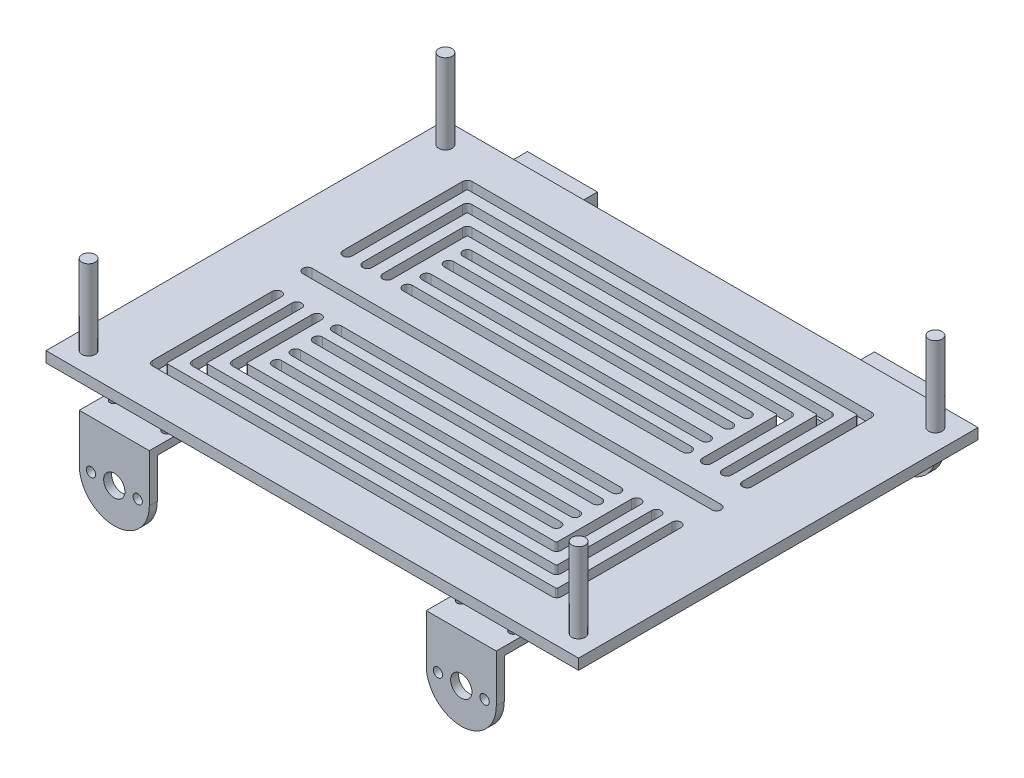
SolidWorks part; units mm, degrees
ref_plane "前基準面" through (0, 0, 0) normal (0, 0, 1) x (1, 0, 0)
ref_plane "上基準面" through (0, 0, 0) normal (0, 1, 0) x (1, 0, 0)
ref_plane "右基準面" through (0, 0, 0) normal (1, 0, 0) x (0, 0, -1)
sketch "草圖1" plane through (0, 0, 0) normal (0, 1, 0) x (1, 0, 0)
  line L0 (0.0511, 0) -> (-99.9489, 0) construction
  line L7 (-99.9489, 75) -> (100.0511, 75)
  line L8 (-99.9489, 75) -> (-99.9489, -75)
  line L9 (-99.9489, -75) -> (100.0511, -75)
  line L10 (100.0511, 75) -> (100.0511, -75)
  line L13 (0.0511, 0) -> (0.0511, 75) construction
  line L14 (-75, 58.25) -> (79.7717, 58.25) construction
  line L15 (-75, 60) -> (75.1022, 60)
  line L16 (-72.75, 56.5) -> (72.8522, 56.5)
  line L17 (-75, 58.25) -> (-75, 13.25) construction
  line L20 (-52.4456, -35.75) -> (52.4456, -35.75) construction
  line L23 (75.1022, 58.25) -> (75.1022, 13.25) construction
  line L29 (-73.25, 56) -> (-73.25, 13.25)
  line L30 (-76.75, 58.25) -> (-76.75, 13.25)
  line L35 (-52.4456, -37.5) -> (52.4456, -37.5)
  line L38 (-67.5, 50.75) -> (67.5, 50.75) construction
  line L39 (-67.5, 52.5) -> (67.5, 52.5)
  line L40 (-65.25, 49) -> (65.25, 49)
  line L41 (-67.5, 50.75) -> (-67.5, 13.25) construction
  line L42 (-65.75, 48.5) -> (-65.75, 13.25)
  line L43 (-69.25, 50.75) -> (-69.25, 13.25)
  line L44 (67.5, 50.75) -> (67.5, 13.25) construction
  line L45 (69.25, 50.75) -> (69.25, 13.25)
  line L46 (65.75, 48.5) -> (65.75, 13.25)
  line L47 (-60, 43.25) -> (60, 43.25) construction
  line L48 (-60, 45) -> (60, 45)
  line L49 (-57.75, 41.5) -> (57.75, 41.5)
  line L50 (-60, 43.25) -> (-60, 13.25) construction
  line L51 (-58.25, 41) -> (-58.25, 13.25)
  line L52 (-61.75, 43.25) -> (-61.75, 13.25)
  line L53 (60, 43.25) -> (60, 13.25) construction
  line L54 (61.75, 43.25) -> (61.75, 13.25)
  line L55 (58.25, 41) -> (58.25, 13.25)
  line L56 (-52.4456, 35.75) -> (52.4456, 35.75) construction
  line L57 (-52.4456, 37.5) -> (52.4456, 37.5)
  line L58 (-52.4456, 34) -> (52.4456, 34)
  line L59 (-52.4456, 28.75) -> (52.4456, 28.75) construction
  line L60 (-52.4456, 30.5) -> (52.4456, 30.5)
  line L61 (-52.4456, 27) -> (52.4456, 27)
  line L62 (-52.4456, 20.4169) -> (52.4456, 20.4169) construction
  line L63 (-52.4456, 22.1669) -> (52.4456, 22.1669)
  line L64 (-52.4456, 18.6669) -> (52.4456, 18.6669)
  line L65 (-52.4456, 13.25) -> (52.4456, 13.25) construction
  line L66 (-52.4456, 15) -> (52.4456, 15)
  line L67 (-52.4456, 11.5) -> (52.4456, 11.5)
  line L68 (76.8522, 58.25) -> (76.8522, 13.25)
  line L69 (73.3522, 56) -> (73.3522, 13.25)
  line L70 (-52.4456, -34) -> (52.4456, -34)
  line L71 (-52.4456, -28.75) -> (52.4456, -28.75) construction
  line L72 (-52.4456, -30.5) -> (52.4456, -30.5)
  line L73 (-52.4456, -27) -> (52.4456, -27)
  line L74 (-52.4456, -20.4169) -> (52.4456, -20.4169) construction
  line L75 (-52.4456, -22.1669) -> (52.4456, -22.1669)
  line L76 (-52.4456, -18.6669) -> (52.4456, -18.6669)
  line L77 (-52.4456, -13.25) -> (52.4456, -13.25) construction
  line L78 (-52.4456, -15) -> (52.4456, -15)
  line L79 (-52.4456, -11.5) -> (52.4456, -11.5)
  line L80 (76.8522, -58.25) -> (76.8522, -13.25)
  line L81 (73.3522, -56) -> (73.3522, -13.25)
  line L82 (69.25, -50.75) -> (69.25, -13.25)
  line L83 (65.75, -48.5) -> (65.75, -13.25)
  line L84 (61.75, -43.25) -> (61.75, -13.25)
  line L85 (58.25, -41) -> (58.25, -13.25)
  line L86 (-67.5, -52.5) -> (67.5, -52.5)
  line L87 (-65.25, -49) -> (65.25, -49)
  line L88 (-60, -45) -> (60, -45)
  line L89 (-57.75, -41.5) -> (57.75, -41.5)
  line L90 (-69.25, -50.75) -> (-69.25, -13.25)
  line L91 (-65.75, -48.5) -> (-65.75, -13.25)
  line L92 (-61.75, -43.25) -> (-61.75, -13.25)
  line L93 (-58.25, -41) -> (-58.25, -13.25)
  line L94 (-73.25, -56) -> (-73.25, -13.25)
  line L95 (-72.75, -56.5) -> (72.8522, -56.5)
  line L96 (-75, -60) -> (75.1022, -60)
  line L97 (-76.75, -58.25) -> (-76.75, -13.25)
  line L98 (-76.75, 0) -> (76.8522, 0) construction
  line L99 (-76.75, 1.75) -> (76.8522, 1.75)
  line L100 (-76.75, -1.75) -> (76.8522, -1.75)
  circle A0 centre (-91.9489, 67) radius 1.5
  circle A1 centre (-91.9489, -67) radius 1.5
  circle A2 centre (92.0511, -67) radius 1.5
  circle A3 centre (92.0511, 67) radius 1.5
  arc A4 (-75, 60) -> (-76.75, 58.25) centre (-75, 58.25) ccw
  arc A14 (-75, 60) -> (-76.75, 58.25) centre (-75, 58.25) ccw
  arc A15 (-76.75, 13.25) -> (-73.25, 13.25) centre (-75, 13.25) ccw
  arc A22 (-73.25, 56) -> (-72.75, 56.5) centre (-72.75, 56) cw
  arc A24 (-52.4456, -37.5) -> (-52.4456, -34) centre (-52.4456, -35.75) cw
  arc A25 (52.4456, -34) -> (52.4456, -37.5) centre (52.4456, -35.75) cw
  arc A26 (-67.5, 52.5) -> (-69.25, 50.75) centre (-67.5, 50.75) ccw
  arc A27 (69.25, 50.75) -> (67.5, 52.5) centre (67.5, 50.75) ccw
  arc A28 (-67.5, 52.5) -> (-69.25, 50.75) centre (-67.5, 50.75) ccw
  arc A29 (-69.25, 13.25) -> (-65.75, 13.25) centre (-67.5, 13.25) ccw
  arc A30 (69.25, 50.75) -> (67.5, 52.5) centre (67.5, 50.75) ccw
  arc A31 (65.75, 13.25) -> (69.25, 13.25) centre (67.5, 13.25) ccw
  arc A32 (-60, 45) -> (-61.75, 43.25) centre (-60, 43.25) ccw
  arc A33 (61.75, 43.25) -> (60, 45) centre (60, 43.25) ccw
  arc A34 (-60, 45) -> (-61.75, 43.25) centre (-60, 43.25) ccw
  arc A35 (-61.75, 13.25) -> (-58.25, 13.25) centre (-60, 13.25) ccw
  arc A36 (61.75, 43.25) -> (60, 45) centre (60, 43.25) ccw
  arc A37 (58.25, 13.25) -> (61.75, 13.25) centre (60, 13.25) ccw
  arc A38 (-52.4456, 37.5) -> (-52.4456, 34) centre (-52.4456, 35.75) ccw
  arc A39 (52.4456, 34) -> (52.4456, 37.5) centre (52.4456, 35.75) ccw
  arc A40 (-52.4456, 30.5) -> (-52.4456, 27) centre (-52.4456, 28.75) ccw
  arc A41 (52.4456, 27) -> (52.4456, 30.5) centre (52.4456, 28.75) ccw
  arc A42 (-52.4456, 22.1669) -> (-52.4456, 18.6669) centre (-52.4456, 20.4169) ccw
  arc A43 (52.4456, 18.6669) -> (52.4456, 22.1669) centre (52.4456, 20.4169) ccw
  arc A44 (-52.4456, 15) -> (-52.4456, 11.5) centre (-52.4456, 13.25) ccw
  arc A45 (52.4456, 11.5) -> (52.4456, 15) centre (52.4456, 13.25) ccw
  arc A47 (75.1022, 60) -> (76.8522, 58.25) centre (75.1022, 58.25) cw
  arc A48 (76.8522, 58.25) -> (75.1022, 60) centre (75.1022, 58.25) ccw
  arc A49 (73.3522, 13.25) -> (76.8522, 13.25) centre (75.1022, 13.25) ccw
  arc A50 (-65.75, 48.5) -> (-65.25, 49) centre (-65.25, 48.5) cw
  arc A51 (-58.25, 41) -> (-57.75, 41.5) centre (-57.75, 41) cw
  arc A52 (58.25, 41) -> (57.75, 41.5) centre (57.75, 41) ccw
  arc A53 (65.75, 48.5) -> (65.25, 49) centre (65.25, 48.5) ccw
  arc A54 (73.3522, 56) -> (72.8522, 56.5) centre (72.8522, 56) ccw
  arc A55 (-52.4456, -30.5) -> (-52.4456, -27) centre (-52.4456, -28.75) cw
  arc A56 (52.4456, -27) -> (52.4456, -30.5) centre (52.4456, -28.75) cw
  arc A57 (-52.4456, -22.1669) -> (-52.4456, -18.6669) centre (-52.4456, -20.4169) cw
  arc A58 (52.4456, -18.6669) -> (52.4456, -22.1669) centre (52.4456, -20.4169) cw
  arc A59 (-52.4456, -15) -> (-52.4456, -11.5) centre (-52.4456, -13.25) cw
  arc A60 (52.4456, -11.5) -> (52.4456, -15) centre (52.4456, -13.25) cw
  arc A61 (58.25, -13.25) -> (61.75, -13.25) centre (60, -13.25) cw
  arc A62 (65.75, -13.25) -> (69.25, -13.25) centre (67.5, -13.25) cw
  arc A63 (73.3522, -13.25) -> (76.8522, -13.25) centre (75.1022, -13.25) cw
  arc A64 (75.1022, -60) -> (76.8522, -58.25) centre (75.1022, -58.25) ccw
  arc A65 (73.3522, -56) -> (72.8522, -56.5) centre (72.8522, -56) cw
  arc A66 (69.25, -50.75) -> (67.5, -52.5) centre (67.5, -50.75) cw
  arc A67 (65.75, -48.5) -> (65.25, -49) centre (65.25, -48.5) cw
  arc A68 (61.75, -43.25) -> (60, -45) centre (60, -43.25) cw
  arc A69 (58.25, -41) -> (57.75, -41.5) centre (57.75, -41) cw
  arc A70 (-58.25, -41) -> (-57.75, -41.5) centre (-57.75, -41) ccw
  arc A71 (-60, -45) -> (-61.75, -43.25) centre (-60, -43.25) cw
  arc A72 (-65.75, -48.5) -> (-65.25, -49) centre (-65.25, -48.5) ccw
  arc A73 (-67.5, -52.5) -> (-69.25, -50.75) centre (-67.5, -50.75) cw
  arc A74 (-61.75, -13.25) -> (-58.25, -13.25) centre (-60, -13.25) cw
  arc A75 (-69.25, -13.25) -> (-65.75, -13.25) centre (-67.5, -13.25) cw
  arc A76 (-76.75, -13.25) -> (-73.25, -13.25) centre (-75, -13.25) cw
  arc A77 (-73.25, -56) -> (-72.75, -56.5) centre (-72.75, -56) ccw
  arc A78 (-75, -60) -> (-76.75, -58.25) centre (-75, -58.25) cw
  arc A79 (-76.75, 1.75) -> (-76.75, -1.75) centre (-76.75, 0) ccw
  arc A80 (76.8522, -1.75) -> (76.8522, 1.75) centre (76.8522, 0) ccw
  point P1 (0, 0)
  point P2 (0, 0)
  point P19 (0, 58.25)
  point P22 (75.1022, 35.75)
  point P26 (-81.708, 35.75)
  point P31 (0, 50.75)
  point P32 (0, -35.75)
  point P34 (68.292, -35.75)
  point P38 (68.292, 35.75)
  point P48 (-6.708, -58.25)
  point P50 (0, -28.75)
  point P55 (0.0511, 0)
  point P70 (-67.5, 32)
  point P75 (67.5, 32)
  point P82 (0, 43.25)
  point P89 (-60, 28.25)
  point P96 (60, 28.25)
  point P105 (0, 35.75)
  point P110 (0, 28.75)
  point P117 (0, 20.4169)
  point P124 (0, 13.25)
  point P137 (0, -20.4169)
  point P144 (0, -13.25)
  dimension "D3" = 3
  dimension "D6" = 8
  dimension "D14" = 0.5
  dimension "D15" = 0.5
  dimension "D16" = 8
  dimension "D17" = 8
  dimension "D19" = 8
  dimension "D7" = 0.5
  dimension "D11" = 0.5
  dimension "D33" = 3
  dimension "D34" = 3
  dimension "D1" = 200
  dimension "D2" = 150
  dimension "D4" = 3.5
  dimension "D5" = 8
  dimension "D8" = 3.5
  dimension "D9" = 15
  dimension "D10" = 3.5
  dimension "D12" = 45
  dimension "D13" = 4
  dimension "D18" = 100
  dimension "D20" = 3.5
  dimension "D21" = 4
  dimension "D22" = 3.5
  dimension "D23" = 3.5
  dimension "D24" = 3.5
  dimension "D25" = 3.5
  dimension "D26" = 4
  dimension "D27" = 3.5
  dimension "D28" = 4
  dimension "D29" = 3.5
  dimension "D30" = 3.5
  dimension "D31" = 4
  dimension "D32" = 16.75
  dimension "D35" = 3.5
extrude "填料-伸長2" add sketch "草圖1" along normal blind 4 contours L10 L7 L8 L9 A45 L67 A44 L66 A43 L64 A42 L63 A41 L61 A40 L60 A39 L58 A38 L57 A1 A0 A2 A3 L70 A25 L35 A24 L55 A52 L49 A51 L51 A35 L52 A32 L48 A33 L54 A37
sketch "草圖2" plane through (0, 0, 0) normal (0, -1, 0) x (1, 0, 0)
  line L0 (0, 0) -> (0, 98.4244) construction
  line L1 (0, 0) -> (-136.3236, 0) construction
  line L2 (-78.3, 66.35) -> (-65.15, 66.35) construction
  line L7 (-78.3, 81.15) -> (-52, 81.15)
  line L8 (-78.3, 81.15) -> (-78.3, 51.55)
  line L9 (-78.3, 51.55) -> (-52, 51.55)
  line L10 (-52, 81.15) -> (-52, 51.55)
  line L11 (-65.15, 47.8631) -> (-65.15, 66.35) construction
  line L12 (-78.3, -51.55) -> (-52, -51.55)
  line L13 (-52, -81.15) -> (-52, -51.55)
  line L14 (-78.3, -81.15) -> (-52, -81.15)
  line L15 (-78.3, -81.15) -> (-78.3, -51.55)
  line L16 (78.3, 51.55) -> (52, 51.55)
  line L17 (52, 81.15) -> (52, 51.55)
  line L18 (78.3, 81.15) -> (52, 81.15)
  line L19 (78.3, 81.15) -> (78.3, 51.55)
  line L20 (78.3, -81.15) -> (78.3, -51.55)
  line L21 (78.3, -81.15) -> (52, -81.15)
  line L22 (52, -81.15) -> (52, -51.55)
  line L23 (78.3, -51.55) -> (52, -51.55)
  circle A1 centre (-75, 58.25) radius 1.5
  circle A2 centre (-65.15, 66.35) radius 5
  circle A3 centre (-55.3, 58.25) radius 1.5
  circle A4 centre (-55.3, 74.45) radius 1.5
  circle A5 centre (-75, 74.45) radius 1.5
  circle A6 centre (-75, -58.25) radius 1.5
  circle A7 centre (-55.3, -58.25) radius 1.5
  circle A8 centre (-55.3, -74.45) radius 1.5
  circle A9 centre (-65.15, -66.35) radius 5
  circle A10 centre (-75, -74.45) radius 1.5
  circle A11 centre (75, 58.25) radius 1.5
  circle A12 centre (55.3, 58.25) radius 1.5
  circle A13 centre (65.15, 66.35) radius 5
  circle A14 centre (55.3, 74.45) radius 1.5
  circle A15 centre (75, 74.45) radius 1.5
  circle A16 centre (75, -74.45) radius 1.5
  circle A17 centre (55.3, -74.45) radius 1.5
  circle A18 centre (65.15, -66.35) radius 5
  circle A19 centre (55.3, -58.25) radius 1.5
  circle A20 centre (75, -58.25) radius 1.5
  dimension "D1" = 3
  dimension "D2" = 3.3
  dimension "D3" = 6.7
  dimension "D4" = 29.6
  dimension "D5" = 26.3
extrude "填料-伸長3" add sketch "草圖2" along normal blind 3
sketch "草圖3" plane through (0, 0, 81.15) normal (0, 0, 1) x (1, 0, 0)
  line L0 (0, 0) -> (0, 39.7303) construction
  line L2 (-78.3, 0) -> (-52, 0)
  line L3 (-78.3, 0) -> (-78.3, -17.9)
  line L5 (-52, 0) -> (-52, -17.9)
  line L6 (-52, 0) -> (-78.3, 0) construction
  line L7 (-65.15, -17.9) -> (-65.15, -13.9) construction
  line L8 (-78.3, -17.9) -> (-52, -17.9) construction
  line L9 (78.3, -17.9) -> (52, -17.9) construction
  line L10 (65.15, -17.9) -> (65.15, -13.9) construction
  line L11 (52, 0) -> (52, -17.9)
  line L12 (78.3, 0) -> (78.3, -17.9)
  line L13 (78.3, 0) -> (52, 0)
  circle A0 centre (-65.15, -17.9) radius 4
  circle A1 centre (-73.925, -17.9) radius 1.75
  circle A2 centre (-56.375, -17.9) radius 1.75
  arc A3 (-78.3, -17.9) -> (-52, -17.9) centre (-65.15, -17.9) ccw
  arc A4 (78.3, -17.9) -> (52, -17.9) centre (65.15, -17.9) cw
  circle A5 centre (56.375, -17.9) radius 1.75
  circle A6 centre (73.925, -17.9) radius 1.75
  circle A7 centre (65.15, -17.9) radius 4
  dimension "D2" = 17.9
  dimension "D3" = 8
  dimension "D4" = 3.5
  dimension "D5" = 4.375
  dimension "D1" = 13.15
extrude "填料-伸長4" add sketch "草圖3" along normal blind 3
sketch "草圖4" plane through (0, 0, -81.15) normal (0, 0, -1) x (-1, 0, 0)
  line L0 (-65.15, -17.9) -> (-65.15, -23.1076) construction
  line L1 (-78.3, 0) -> (-52, 0)
  line L2 (-78.3, 0) -> (-78.3, -17.9)
  line L4 (-52, 0) -> (-52, -17.9)
  line L5 (0, 0) -> (0, 31.3223) construction
  line L6 (65.15, -17.9) -> (65.15, -23.1076) construction
  line L7 (52, 0) -> (52, -17.9)
  line L8 (78.3, 0) -> (78.3, -17.9)
  line L9 (78.3, 0) -> (52, 0)
  arc A0 (-78.3, -17.9) -> (-52, -17.9) centre (-65.15, -17.9) ccw
  circle A1 centre (-65.15, -17.9) radius 4
  circle A2 centre (-73.925, -17.9) radius 1.75
  circle A3 centre (-56.375, -17.9) radius 1.75
  circle A4 centre (56.375, -17.9) radius 1.75
  circle A5 centre (73.925, -17.9) radius 1.75
  circle A6 centre (65.15, -17.9) radius 4
  arc A7 (78.3, -17.9) -> (52, -17.9) centre (65.15, -17.9) cw
  dimension "D1" = 8
  dimension "D4" = 3.5
  dimension "D2" = 13.15
  dimension "D3" = 4.375
extrude "填料-伸長5" add sketch "草圖4" along normal blind 3
sketch "草圖5" plane through (0, 4, 0) normal (0, 1, 0) x (1, 0, 0)
  circle A0 centre (-91.9489, 67) radius 2.5
  circle A1 centre (92.0511, 67) radius 2.5
  circle A2 centre (92.0511, -67) radius 2.5
  circle A3 centre (-91.9489, -67) radius 2.5
extrude "填料-伸長6" add sketch "草圖5" along normal blind 30 separate body
